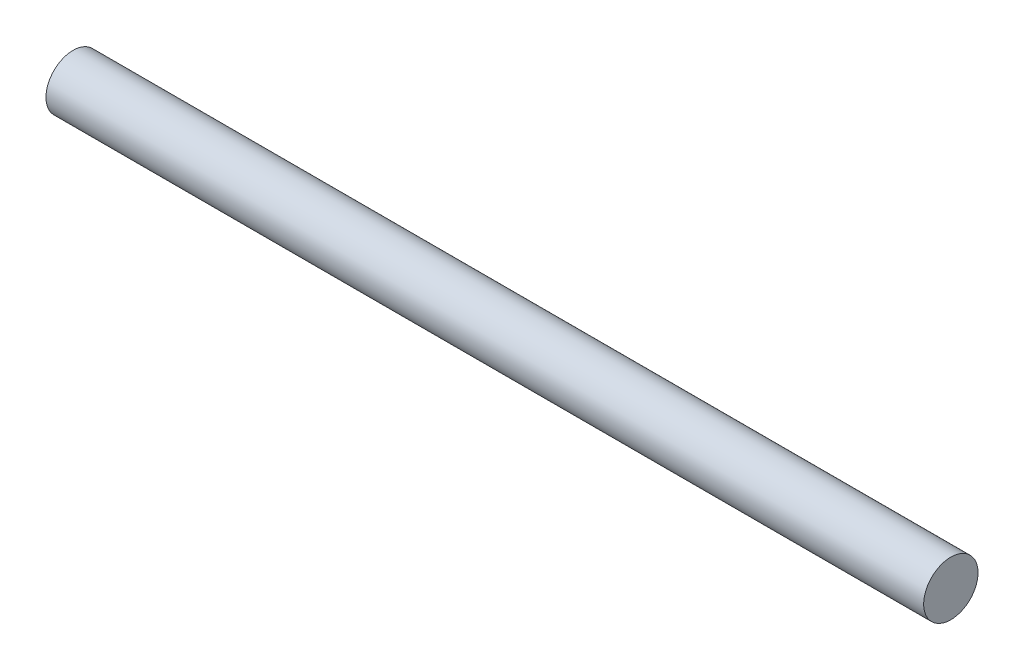
SolidWorks part; units mm, degrees
ref_plane "Front Plane" through (0, 0, 0) normal (0, 0, 1) x (1, 0, 0)
ref_plane "Top Plane" through (0, 0, 0) normal (0, 1, 0) x (1, 0, 0)
ref_plane "Right Plane" through (0, 0, 0) normal (1, 0, 0) x (0, 0, -1)
sketch "Sketch1" plane through (0, 0, 0) normal (1, 0, 0) x (0, 0, -1)
  circle A0 centre (0, 0) radius 16.51
  dimension "D1" = 33.02
extrude "Boss-Extrude1" add sketch "Sketch1" along normal blind 533.4
